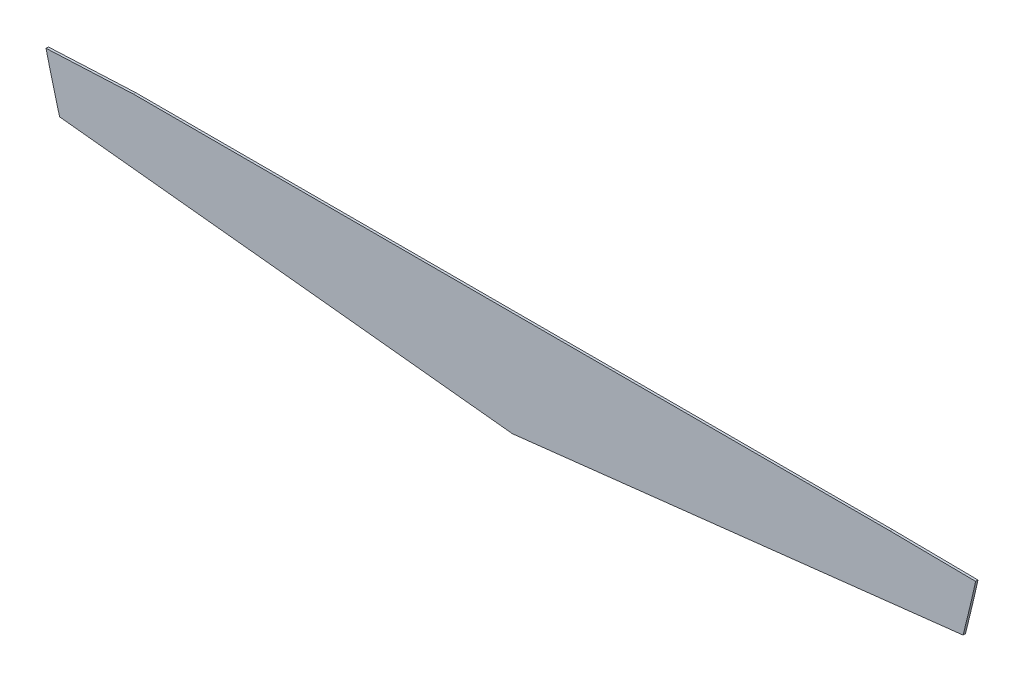
SolidWorks part; units mm, degrees
ref_plane "Alzado" through (0, 0, 0) normal (0, 0, 1) x (1, 0, 0)
ref_plane "Planta" through (0, 0, 0) normal (0, 1, 0) x (1, 0, 0)
ref_plane "Vista lateral" through (0, 0, 0) normal (1, 0, 0) x (0, 0, -1)
sketch "Model" plane through (0, 0, 0) normal (0, 0, 1) x (1, 0, 0)
  line L0 (47.9003, -3.8807) -> (15.9003, -3.8807)
  line L1 (15.9003, -3.8807) -> (12.2026, -4.0527)
  line L2 (47.9003, -3.8807) -> (51.5214, -3.9193)
  line L3 (31.9257, -8.3084) -> (50.9904, -6.1529)
  line L4 (12.7786, -6.2783) -> (31.9257, -8.3084)
  arc A0 (50.9904, -6.1529) -> (51.5214, -3.9193) centre (-28.4151, 13.9042) ccw
  arc A1 (12.2026, -4.0527) -> (12.7786, -6.2783) centre (83.1941, 13.1331) ccw
extrude "Saliente-Extruir1" add sketch "Model" along normal blind 0.1
